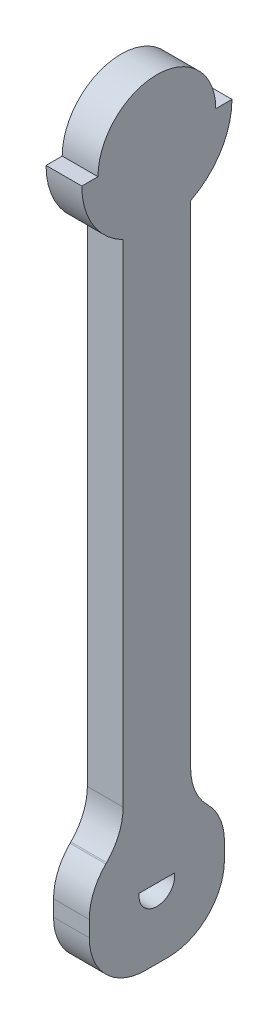
SolidWorks part; units mm, degrees
ref_plane "Front Plane" through (0, 0, 0) normal (0, 0, 1) x (1, 0, 0)
ref_plane "Top Plane" through (0, 0, 0) normal (0, 1, 0) x (1, 0, 0)
ref_plane "Right Plane" through (0, 0, 0) normal (1, 0, 0) x (0, 0, -1)
sketch "Sketch1" plane through (0, 0, 0) normal (1, 0, 0) x (0, 0, -1)
  line L0 (3.4925, 0) -> (-3.4925, 0) construction
  line L1 (-3.1464, 6.425) -> (3.1464, 6.425)
  line L2 (0, 3.4925) -> (0, -3.4925) construction
  line L3 (-6, 120.3) -> (6, 120.3)
  line L4 (-6, 120.3) -> (-6, 0)
  line L5 (-6, 0) -> (6, 0) construction
  line L6 (6, 120.3) -> (6, 0)
  line L7 (-6, 120.3) -> (6, 0) construction
  line L8 (-6, 0) -> (6, 120.3) construction
  line L9 (-10.4648, 120.3) -> (-10.4648, 112.035)
  line L10 (10.4648, 120.3) -> (10.4648, 112.035)
  line L11 (-10.4648, 120.3) -> (-13.335, 120.3)
  line L12 (10.4648, 120.3) -> (13.335, 120.3)
  line L13 (-6, 16.9706) -> (-12, 10.9706)
  line L14 (-12, 10.9706) -> (-12, -6)
  line L15 (-12, -6) -> (12, -6)
  line L16 (12, -6) -> (12, 10.9706)
  line L17 (12, 10.9706) -> (6, 16.9706)
  line L18 (0, 6) -> (0, -6) construction
  circle A0 centre (0, 6) radius 3.175
  circle A1 centre (0, 120.3) radius 13.335
  circle A2 centre (0, 120.3) radius 10.4648
  point P4 (0, 60.15)
  point P13 (0, 2.825)
  dimension "D1" = 6.35
  dimension "D5" = 3.6
  dimension "D6" = 26.67
  dimension "D7" = 20.9296
  dimension "D2" = 12
  dimension "D3" = 6
  dimension "D4" = 114.3
  dimension "D8" = 24
  dimension "D9" = 12
  dimension "D10" = 12
  dimension "D11" = 45
  dimension "D12" = 45
  dimension "D13" = 12
extrude "Boss-Extrude1" add sketch "Sketch1" along normal blind 6.35 contours L6 L3 L4 L5 A0 | L1 A0 | L4 A2 L6 L3 | A2 L4 A1 L6 | L6 A2 L4 L3 | A2 L9 A1 L4 | A2 L6 A1 L10 | L11 A1 L9 | L10 A1 L12
fillet "Fillet1" radius 10 6 edges at (3.175, 16.9706, -6) (3.175, 10.9706, -12) (3.175, -6, -12) (3.175, -6, 12) (3.175, 10.9706, 12) (3.175, 16.9706, 6)
